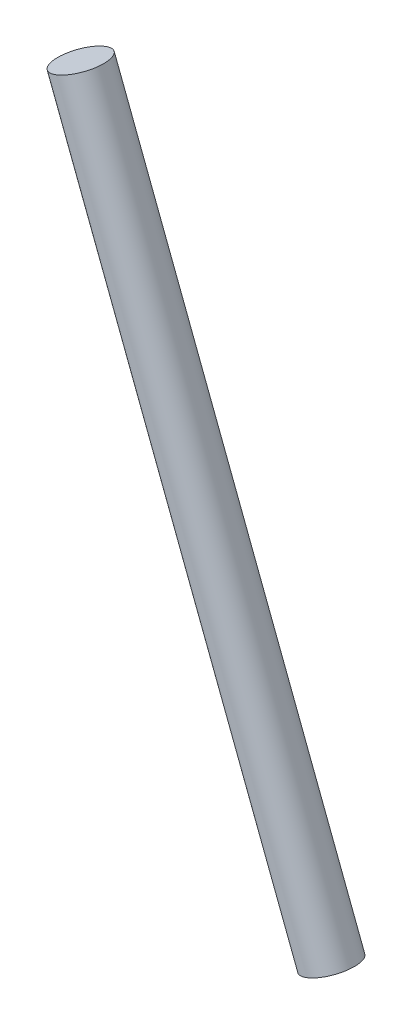
SolidWorks part; units mm, degrees
ref_plane "Front Plane" through (0, 0, 0) normal (0, 0, 1) x (1, 0, 0)
ref_plane "Top Plane" through (0, 0, 0) normal (0, 1, 0) x (1, 0, 0)
ref_plane "Right Plane" through (0, 0, 0) normal (1, 0, 0) x (0, 0, -1)
sketch "Sketch1" plane through (0, 0, 0) normal (0, 0, 1) x (1, 0, 0)
  line L0 (536.0759, 722.924) -> (613.7007, 519.6096)
  line L1 (528.9571, 720.206) -> (606.5819, 516.8916)
  line L2 (528.9571, 720.206) -> (536.0759, 722.924)
  line L3 (606.5819, 516.8916) -> (613.7007, 519.6096)
  dimension "D1" = 7.62
revolve "Revolve1" add sketch "Sketch1" angle 360 about L0
